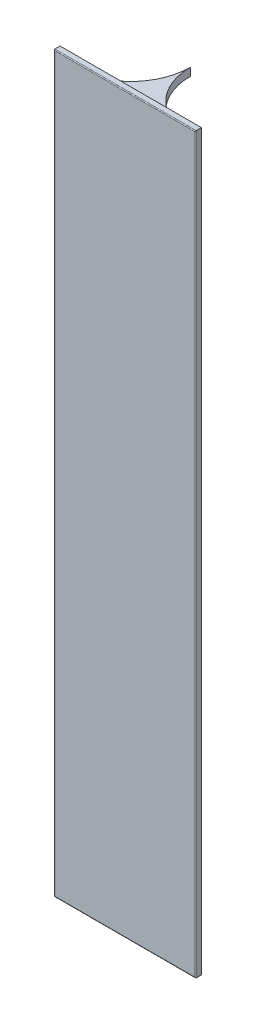
SolidWorks part; units mm, degrees
ref_plane "Front Plane" through (0, 0, 0) normal (0, 0, 1) x (1, 0, 0)
ref_plane "Top Plane" through (0, 0, 0) normal (0, 1, 0) x (1, 0, 0)
ref_plane "Right Plane" through (0, 0, 0) normal (1, 0, 0) x (0, 0, -1)
sketch "Sketch1" plane through (0, 0, 0) normal (0, 0, 1) x (1, 0, 0)
  line L0 (-18, 92.4) -> (-18, -92.4) construction
  line L1 (-17.8, 92.4) -> (17.8, 92.4)
  line L2 (-17.8, 92.4) -> (-17.8, -92.4)
  line L3 (-17.8, -92.4) -> (17.8, -92.4)
  line L4 (17.8, 92.4) -> (17.8, -92.4)
  line L5 (-17.8, 92.4) -> (17.8, -92.4) construction
  line L6 (-17.8, -92.4) -> (17.8, 92.4) construction
  line L7 (-18, -92.4) -> (-168, -92.4) construction
  point P0 (0, 0)
  dimension "D2" = 0.2
extrude "Boss-Extrude1" add sketch "Sketch1" along normal blind 1.5
fillet "Fillet1" radius 0.2 4 edges at (0, -92.4, 1.5) (-17.8, 0, 1.5) (0, 92.4, 1.5) (17.8, 0, 1.5)
sketch "Sketch2" plane through (0, 89.167, 0) normal (0, 1, 0) x (1, 0, 0)
  line L0 (0, 0) -> (0, 15.6) construction
  line L1 (14.8137, 0.0012) -> (-14.8137, 0.0012)
  arc A0 (14.8137, 0.0012) -> (0, 15) centre (15, 15) cw
  arc A2 (-13.4119, 0.0843) -> (-0.1496, 12.8871) centre (-15, 15) ccw construction
  arc A3 (-14.8137, 0.0012) -> (0, 15) centre (-15, 15) ccw
  arc A4 (-15, 0) -> (-13.4119, 0.0843) centre (-15, 15) ccw construction
extrude "Boss-Extrude2" add sketch "Sketch2" against normal blind 2
